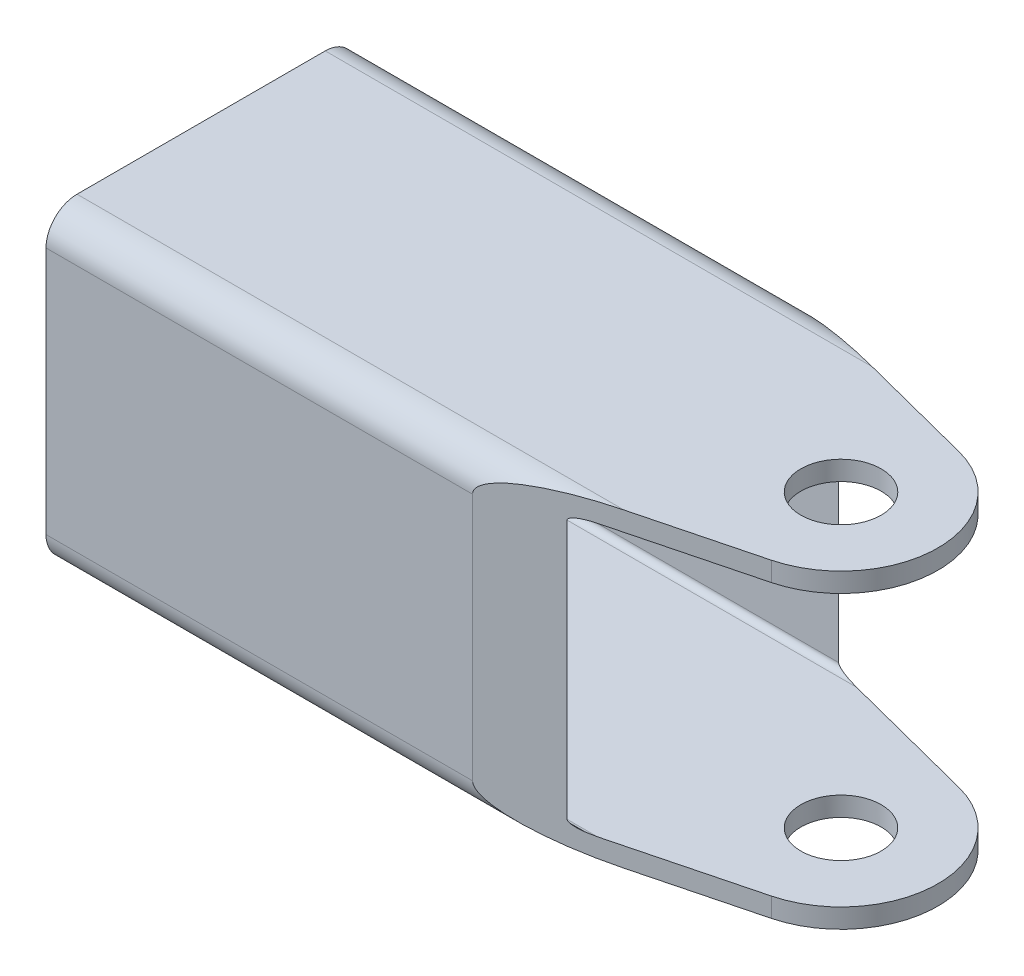
SolidWorks part; units mm, degrees
material "AISI 4130 Steel, annealed at 865C"
ref_plane "Front Plane" through (0, 0, 0) normal (0, 0, 1) x (1, 0, 0)
ref_plane "Top Plane" through (0, 0, 0) normal (0, 1, 0) x (1, 0, 0)
ref_plane "Right Plane" through (0, 0, 0) normal (1, 0, 0) x (0, 0, -1)
sketch "Sketch1" plane through (0, 0, 0) normal (1, 0, 0) x (0, 0, -1)
  line L1 (-10.16, 12.7) -> (10.16, 12.7)
  line L2 (-12.7, 10.16) -> (-12.7, -10.16)
  line L3 (-10.16, -12.7) -> (10.16, -12.7)
  line L4 (12.7, 10.16) -> (12.7, -10.16)
  arc A0 (-10.16, 12.7) -> (-12.7, 10.16) centre (-10.16, 10.16) ccw
  arc A1 (-10.16, -12.7) -> (-12.7, -10.16) centre (-10.16, -10.16) cw
  arc A2 (10.16, 12.7) -> (12.7, 10.16) centre (10.16, 10.16) cw
  arc A3 (12.7, -10.16) -> (10.16, -12.7) centre (10.16, -10.16) cw
  point P4 (0, -12.7)
  point P7 (0, 0)
  point P15 (12.7, 0)
  dimension "D3" = 2.54
  dimension "D4" = 2.54
  dimension "D5" = 2.54
  dimension "D6" = 2.54
  dimension "D1" = 25.4
  dimension "D2" = 20.32
extrude "Boss-Extrude1" add sketch "Sketch1" along normal blind 25.4 and the other way blind 34.925
sketch "Sketch11" plane through (25.4, 0, 0) normal (1, 0, 0) x (0, 0, -1)
  line L0 (-10.16, -12.7) -> (10.16, -12.7) construction
  line L1 (-10.6045, 11.1125) -> (10.6045, 11.1125)
  line L2 (-11.1125, 10.6045) -> (-11.1125, -10.6045)
  line L3 (-10.6045, -11.1125) -> (10.6045, -11.1125)
  line L4 (11.1125, 10.6045) -> (11.1125, -10.6045)
  line L5 (10.16, 12.7) -> (-10.16, 12.7) construction
  line L6 (12.7, -10.16) -> (12.7, 10.16) construction
  line L7 (-12.7, 10.16) -> (-12.7, -10.16) construction
  arc A0 (10.6045, 11.1125) -> (11.1125, 10.6045) centre (10.6045, 10.6045) cw
  arc A1 (10.6045, -11.1125) -> (11.1125, -10.6045) centre (10.6045, -10.6045) ccw
  arc A2 (-11.1125, -10.6045) -> (-10.6045, -11.1125) centre (-10.6045, -10.6045) ccw
  arc A3 (-10.6045, 11.1125) -> (-11.1125, 10.6045) centre (-10.6045, 10.6045) ccw
  dimension "D1" = 1.5875
  dimension "D2" = 1.5875
  dimension "D3" = 1.5875
  dimension "D4" = 1.5875
  dimension "D5" = 0.508
extrude "Cut-Extrude4" cut sketch "Sketch11" against normal through all
sketch "Sketch12" plane through (0, 12.7, 0) normal (0, 1, 0) x (1, 0, 0)
  line L1 (0, 12.7) -> (50.8, 12.7)
  line L2 (50.8, 12.7) -> (50.8, -12.7)
  line L12 (50.8, -12.7) -> (0, -12.7)
  line L13 (19.4444, -7.6861) -> (0, -12.7)
  line L14 (19.4444, 7.6861) -> (0, 12.7)
  line L15 (-34.925, -12.7) -> (25.4, -12.7) construction
  line L16 (-34.925, 12.7) -> (25.4, 12.7) construction
  line L18 (25.4, 10.16) -> (25.4, -10.16) construction
  arc A1 (19.4444, -7.6861) -> (19.4444, 7.6861) centre (17.4625, 0) ccw
  point P8 (18.1688, 9.2165)
  dimension "D2" = 50.8
  dimension "D1" = 17.4625
extrude "Cut-Extrude5" cut sketch "Sketch12" against normal through all
sketch "Sketch14" plane through (0, 12.7, 0) normal (0, 1, 0) x (1, 0, 0)
  circle A0 centre (17.4625, 0) radius 3.2893
  arc A2 (19.4444, -7.6861) -> (19.4444, 7.6861) centre (17.4625, 0) ccw construction
  point P0 (17.4625, 0)
  point P6 (25.4, 0)
  dimension "D2" = 6.5786
  dimension "D1" = 7.9375
  dimension "D3" = 17.4625
extrude "Cut-Extrude6" cut sketch "Sketch14" against normal through all
